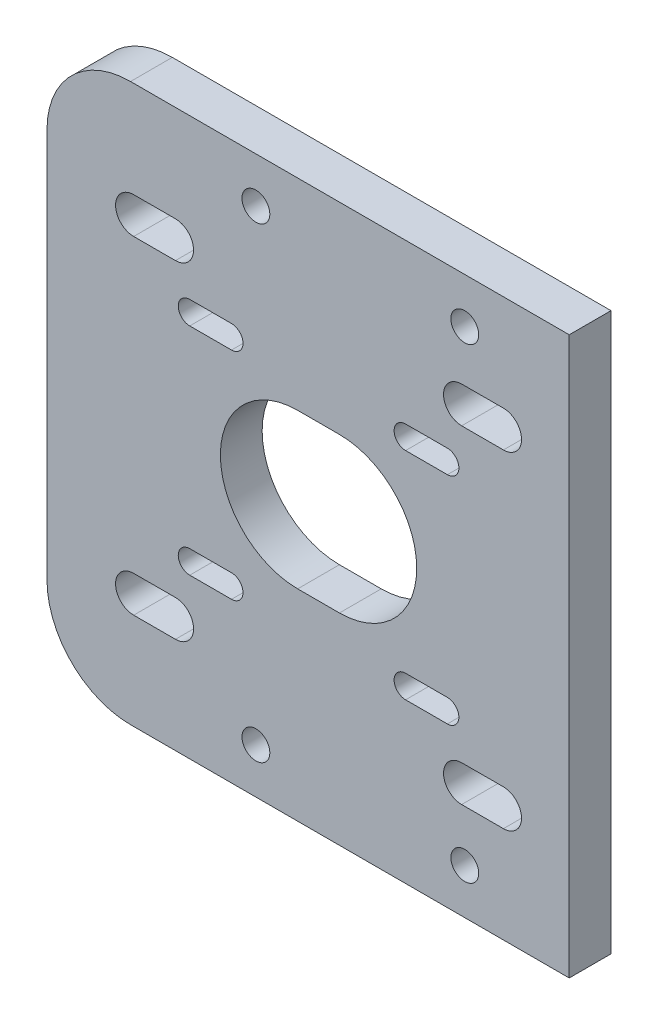
SolidWorks part; units mm, degrees
ref_plane "Alzado" through (0, 0, 0) normal (0, 0, 1) x (1, 0, 0)
ref_plane "Planta" through (0, 0, 0) normal (0, 1, 0) x (1, 0, 0)
ref_plane "Vista lateral" through (0, 0, 0) normal (1, 0, 0) x (0, 0, -1)
sketch "Croquis1" plane through (0, 0, 0) normal (0, 0, 1) x (1, 0, 0)
  line L1 (0, 0) -> (75, 0)
  line L2 (0, 0) -> (0, 80)
  line L3 (0, 80) -> (75, 80)
  line L4 (75, 0) -> (75, 80)
  dimension "D1" = 80
  dimension "D2" = 75
extrude "Saliente-Extruir1" add sketch "Croquis1" along normal blind 6
sketch "Croquis2" plane through (0, 0, 0) normal (0, 0, -1) x (-1, 0, 0)
  line L0 (0, 80) -> (0, 0) construction
  line L1 (0, 40) -> (-75, 40) construction
  line L4 (-75, 0) -> (-75, 80) construction
  line L7 (-36, 40) -> (-42, 40) construction
  line L10 (-36, 28.9) -> (-42, 28.9)
  line L19 (-36, 51.1) -> (-42, 51.1)
  line L20 (-20.5, 24.5) -> (-26.5, 24.5) construction
  line L21 (-20.5, 22.85) -> (-26.5, 22.85)
  line L22 (-20.5, 26.15) -> (-26.5, 26.15)
  line L23 (-51.5, 55.5) -> (-57.5, 55.5) construction
  line L24 (-51.5, 53.85) -> (-57.5, 53.85)
  line L25 (-51.5, 57.15) -> (-57.5, 57.15)
  line L26 (-51.5, 24.5) -> (-57.5, 24.5) construction
  line L27 (-51.5, 22.85) -> (-57.5, 22.85)
  line L28 (-51.5, 26.15) -> (-57.5, 26.15)
  line L29 (-20.5, 55.5) -> (-26.5, 55.5) construction
  line L30 (-20.5, 53.85) -> (-26.5, 53.85)
  line L31 (-20.5, 57.15) -> (-26.5, 57.15)
  line L32 (-12.45, 16.45) -> (-18.45, 16.45) construction
  line L33 (-12.45, 13.85) -> (-18.45, 13.85)
  line L34 (-12.45, 19.05) -> (-18.45, 19.05)
  line L35 (-59.55, 16.45) -> (-65.55, 16.45) construction
  line L36 (-15.45, 63.55) -> (-62.55, 63.55) construction
  line L37 (-15.45, 63.55) -> (-15.45, 16.45) construction
  line L38 (-15.45, 16.45) -> (-62.55, 16.45) construction
  line L39 (-62.55, 63.55) -> (-62.55, 16.45) construction
  line L40 (-15.45, 63.55) -> (-62.55, 16.45) construction
  line L41 (-15.45, 16.45) -> (-62.55, 63.55) construction
  line L42 (-59.55, 13.85) -> (-65.55, 13.85)
  line L43 (-59.55, 19.05) -> (-65.55, 19.05)
  line L44 (-12.45, 63.55) -> (-18.45, 63.55) construction
  line L45 (-12.45, 60.95) -> (-18.45, 60.95)
  line L46 (-12.45, 66.15) -> (-18.45, 66.15)
  line L47 (-59.55, 63.55) -> (-65.55, 63.55) construction
  line L48 (-59.55, 60.95) -> (-65.55, 60.95)
  line L49 (-59.55, 66.15) -> (-65.55, 66.15)
  arc A19 (-36, 28.9) -> (-36, 51.1) centre (-36, 40) ccw
  arc A20 (-42, 51.1) -> (-42, 28.9) centre (-42, 40) ccw
  arc A21 (-20.5, 22.85) -> (-20.5, 26.15) centre (-20.5, 24.5) ccw
  arc A22 (-26.5, 26.15) -> (-26.5, 22.85) centre (-26.5, 24.5) ccw
  arc A23 (-51.5, 53.85) -> (-51.5, 57.15) centre (-51.5, 55.5) ccw
  arc A24 (-57.5, 57.15) -> (-57.5, 53.85) centre (-57.5, 55.5) ccw
  arc A25 (-51.5, 22.85) -> (-51.5, 26.15) centre (-51.5, 24.5) ccw
  arc A26 (-57.5, 26.15) -> (-57.5, 22.85) centre (-57.5, 24.5) ccw
  arc A27 (-20.5, 53.85) -> (-20.5, 57.15) centre (-20.5, 55.5) ccw
  arc A28 (-26.5, 57.15) -> (-26.5, 53.85) centre (-26.5, 55.5) ccw
  arc A29 (-12.45, 13.85) -> (-12.45, 19.05) centre (-12.45, 16.45) ccw
  arc A30 (-18.45, 19.05) -> (-18.45, 13.85) centre (-18.45, 16.45) ccw
  arc A31 (-59.55, 13.85) -> (-59.55, 19.05) centre (-59.55, 16.45) ccw
  arc A32 (-65.55, 19.05) -> (-65.55, 13.85) centre (-65.55, 16.45) ccw
  arc A33 (-12.45, 60.95) -> (-12.45, 66.15) centre (-12.45, 63.55) ccw
  arc A34 (-18.45, 66.15) -> (-18.45, 60.95) centre (-18.45, 63.55) ccw
  arc A35 (-59.55, 60.95) -> (-59.55, 66.15) centre (-59.55, 63.55) ccw
  arc A36 (-65.55, 66.15) -> (-65.55, 60.95) centre (-65.55, 63.55) ccw
  point P6 (-39, 40)
  point P12 (-15.45, 16.45)
  point P19 (-23.5, 24.5)
  point P28 (-54.5, 55.5)
  point P35 (-54.5, 24.5)
  point P40 (-39, 40)
  point P48 (-23.5, 55.5)
  point P56 (-62.55, 16.45)
  point P63 (-15.45, 63.55)
  point P70 (-62.55, 63.55)
  dimension "D2" = 6
  dimension "D3" = 11.1
  dimension "D4" = 3.3
  dimension "D5" = 6
  dimension "D6" = 36
  dimension "D13" = 47.1
  dimension "D14" = 47.1
  dimension "D12" = 5.2
  dimension "D7" = 15.5
  dimension "D8" = 15.5
  dimension "D9" = 3.3
  dimension "D10" = 6
  dimension "D11" = 6
  dimension "D15" = 6
  dimension "D16" = 6
  dimension "D17" = 3.3
  dimension "D18" = 6
  dimension "D19" = 3.3
  dimension "D20" = 6
  dimension "D21" = 15.5
  dimension "D22" = 15.5
  dimension "D23" = 15.5
  dimension "D24" = 15.5
  dimension "D25" = 15.5
  dimension "D26" = 15.5
  dimension "D27" = 6
  dimension "D28" = 5.2
  dimension "D29" = 5.2
  dimension "D30" = 5.2
extrude "Cortar-Extruir1" cut sketch "Croquis2" against normal through all
fillet "Redondeo1" radius 12 2 edges at (0, 0, 3) (0, 80, 3)
sketch "Croquis3" plane through (0, 0, 0) normal (0, 0, -1) x (-1, 0, 0)
  line L0 (-75, 0) -> (-75, 80) construction
  line L1 (-12, 0) -> (-75, 0) construction
  line L2 (-75, 80) -> (-12, 80) construction
  circle A0 centre (-60, 6.5) radius 2
  circle A1 centre (-30, 6.5) radius 2
  circle A2 centre (-60, 73.5) radius 2
  circle A3 centre (-30, 73.5) radius 2
  dimension "D1" = 4
  dimension "D2" = 15
  dimension "D3" = 45
  dimension "D4" = 15
  dimension "D5" = 45
  dimension "D6" = 6.5
  dimension "D7" = 6.5
  dimension "D8" = 6.5
  dimension "D9" = 6.5
extrude "Cortar-Extruir2" cut sketch "Croquis3" against normal through all
